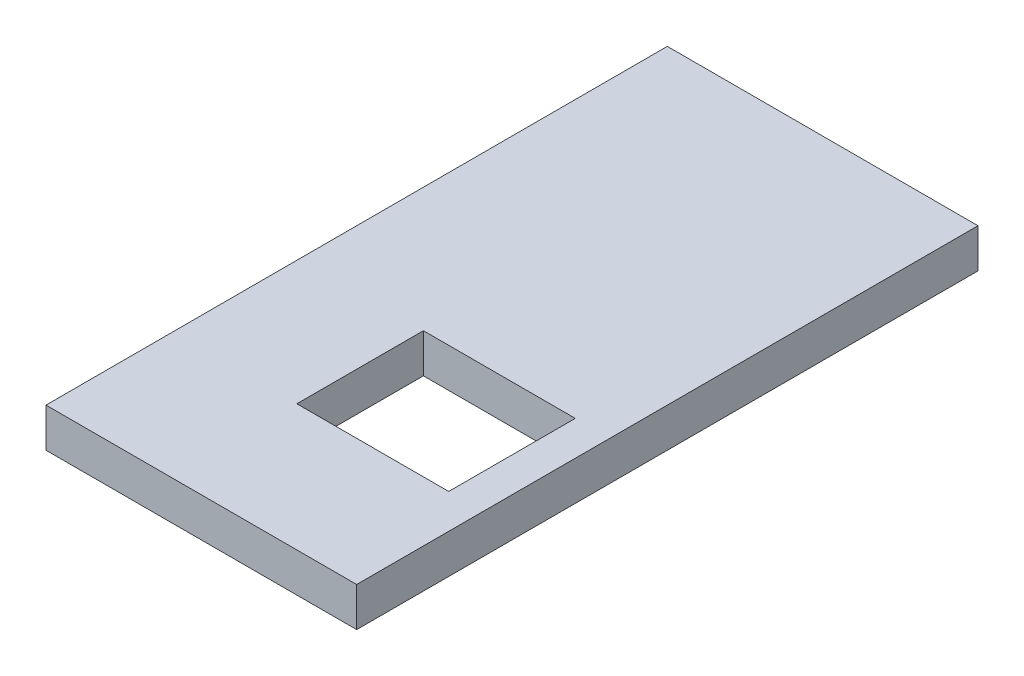
SolidWorks part; units mm, degrees
ref_plane "Plano frontal" through (0, 0, 0) normal (0, 0, 1) x (1, 0, 0)
ref_plane "Plano superior" through (0, 0, 0) normal (0, 1, 0) x (1, 0, 0)
ref_plane "Plano direito" through (0, 0, 0) normal (1, 0, 0) x (0, 0, -1)
sketch "Esboço1" plane through (0, 0, 0) normal (0, 0, 1) x (1, 0, 0)
  line L1 (0, 0) -> (1350, 0)
  line L2 (0, 0) -> (0, 170)
  line L3 (0, 170) -> (1350, 170)
  line L4 (1350, 0) -> (1350, 170)
  dimension "D1" = 170
  dimension "D2" = 1350
extrude "Ressalto-extrusão1" add sketch "Esboço1" along normal blind 2700
sketch "Esboço2" plane through (0, 170, 0) normal (0, 1, 0) x (1, 0, 0)
  line L0 (1350, -2700) -> (1350, 0) construction
  line L1 (540, -1600) -> (1200, -1600)
  line L2 (540, -1600) -> (540, -2150)
  line L3 (540, -2150) -> (1200, -2150)
  line L4 (1200, -1600) -> (1200, -2150)
  line L6 (1350, 0) -> (0, 0) construction
  dimension "D1" = 660
  dimension "D2" = 150
  dimension "D3" = 550
  dimension "D4" = 1600
extrude "Corte-extrusão1" cut sketch "Esboço2" against normal through all
equation "\"17vm\"=150"
